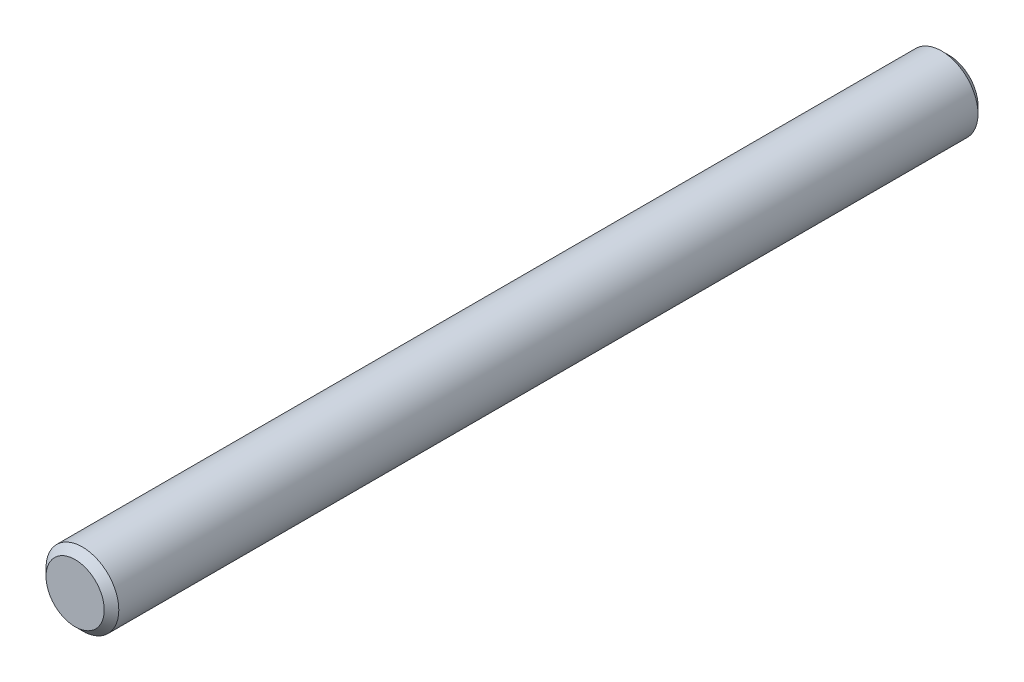
SolidWorks part; units mm, degrees
ref_plane "Front" through (0, 0, 0) normal (0, 0, 1) x (1, 0, 0)
ref_plane "Top" through (0, 0, 0) normal (0, 1, 0) x (1, 0, 0)
ref_plane "Right" through (0, 0, 0) normal (1, 0, 0) x (0, 0, -1)
sketch "Sketch1" plane through (0, 0, 0) normal (0, 0, 1) x (1, 0, 0)
  circle A0 centre (0, 0) radius 3.175
  dimension "dia" = 6.35
sketch "Sketch2" plane through (0, 0, 0) normal (1, 0, 0) x (0, 0, -1)
  line L0 (-38.1, 0) -> (38.1, 0) construction
  line L1 (5.2388, 0) -> (-5.2388, 0) construction
  line L3 (38.1, 3.175) -> (38.1, -3.175) construction
  line L4 (-38.1, 3.175) -> (-38.1, -3.175) construction
  line L5 (-19.05, 3.175) -> (-19.05, -3.175) construction
  line L6 (19.05, 3.175) -> (19.05, -3.175) construction
  point P6 (0, 0)
  point P10 (38.1, 0)
  point P13 (-38.1, 0)
  point P16 (-19.05, 0)
  point P19 (19.05, 0)
  dimension "lg" = 76.2
  dimension "D2" = 19.05
  dimension "D3" = 19.05
sketch "Sketch3" plane through (0, 0, 0) normal (0, 0, 1) x (1, 0, 0)
  line L0 (0, 3.175) -> (0, -3.175) construction
  circle A0 centre (0, 0) radius 3.175
extrude "Boss-Extrude1" add sketch "Sketch3" along normal mid plane 76.2
chamfer "Chamfer1" distance 0.635 angle 45 2 edges at (3.175, 0, -38.1) (3.175, 0, 38.1)
equation "\"D1@Sketch2\"=\"dia@sketch1\""
equation "\"D1@Sketch3\"=\"dia@Sketch1\""
equation "\"D1@Boss-Extrude1\"=\"lg@Sketch2\""
equation "\"D1@Chamfer1\"=\"dia@Sketch1\"*.1"
